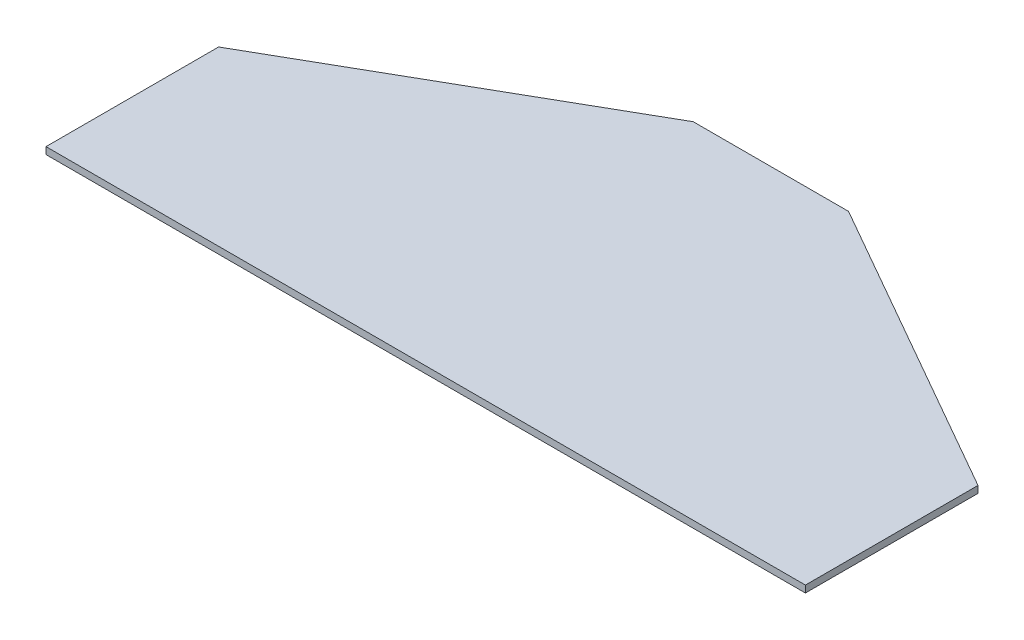
SolidWorks part; units mm, degrees
material "Thornel Mat VMA"
ref_plane "Front Plane" through (0, 0, 0) normal (0, 0, 1) x (1, 0, 0)
ref_plane "Top Plane" through (0, 0, 0) normal (0, 1, 0) x (1, 0, 0)
ref_plane "Right Plane" through (0, 0, 0) normal (1, 0, 0) x (0, 0, -1)
sketch "Sketch1" plane through (0, 0, 0) normal (0, 1, 0) x (1, 0, 0)
  line L0 (-139.7, 0) -> (139.7, 0)
  line L1 (139.7, 0) -> (139.7, 63.5)
  line L2 (139.7, 63.5) -> (28.575, 127)
  line L4 (-28.575, 127) -> (-139.7, 63.5)
  line L5 (-139.7, 63.5) -> (-139.7, 0)
  line L6 (-132.08, 7.62) -> (-34.1377, 7.62) construction
  line L7 (132.08, 7.62) -> (132.08, 59.0779) construction
  line L8 (132.08, 59.0779) -> (92.3839, 81.7614) construction
  line L9 (26.5514, 119.38) -> (24.4475, 119.38) construction
  line L10 (-26.5514, 119.38) -> (-85.696, 85.5831) construction
  line L11 (-132.08, 59.0779) -> (-132.08, 7.62) construction
  line L12 (-24.4475, 119.38) -> (-24.4475, 7.62) construction
  line L13 (-16.8275, 7.62) -> (-16.8275, 119.38) construction
  line L14 (16.8275, 7.62) -> (16.8275, 119.38) construction
  line L15 (24.4475, 7.62) -> (24.4475, 119.38) construction
  line L16 (0, -21.6733) -> (0, 35.7477) construction
  line L17 (-24.4475, 119.38) -> (-26.5514, 119.38) construction
  line L18 (16.8275, 119.38) -> (-16.8275, 119.38) construction
  line L19 (-16.8275, 7.62) -> (16.8275, 7.62) construction
  line L20 (34.1377, 7.62) -> (132.08, 7.62) construction
  line L30 (28.575, 127) -> (-28.575, 127)
  line L31 (-34.1377, 7.62) -> (-92.3839, 81.7614) construction
  line L32 (-85.696, 85.5831) -> (-24.4475, 7.62) construction
  line L33 (24.4475, 7.62) -> (85.696, 85.5831) construction
  line L34 (92.3839, 81.7614) -> (34.1377, 7.62) construction
  line L35 (-92.3839, 81.7614) -> (-132.08, 59.0779) construction
  line L36 (85.696, 85.5831) -> (26.5514, 119.38) construction
  point P10 (0, 0)
  point P25 (-79.3157, 89.229)
  point P28 (0, 0)
  point P32 (-24.4475, 14.1171)
  point P33 (-24.4475, 15.4358)
  point P34 (-35.7328, 7.62)
  point P35 (-24.4475, 5.5607)
  point P36 (34.2755, 7.62)
  point P37 (-90.9259, 82.5945)
  dimension "D2" = 279.4
  dimension "D3" = 57.15
  dimension "D4" = 63.5
  dimension "D5" = 7.62
  dimension "D6" = 7.62
  dimension "D7" = 7.62
  dimension "D8" = 127
  dimension "D9" = 7.62
  dimension "D10" = 7.62
  dimension "D11" = 7.62
  dimension "D12" = 7.62
  dimension "D13" = 41.275
  dimension "D14" = 7.62
  dimension "D15" = 7.62
  dimension "D16" = 45.72
extrude "Boss-Extrude1" add sketch "Sketch1" along normal blind 2.54
